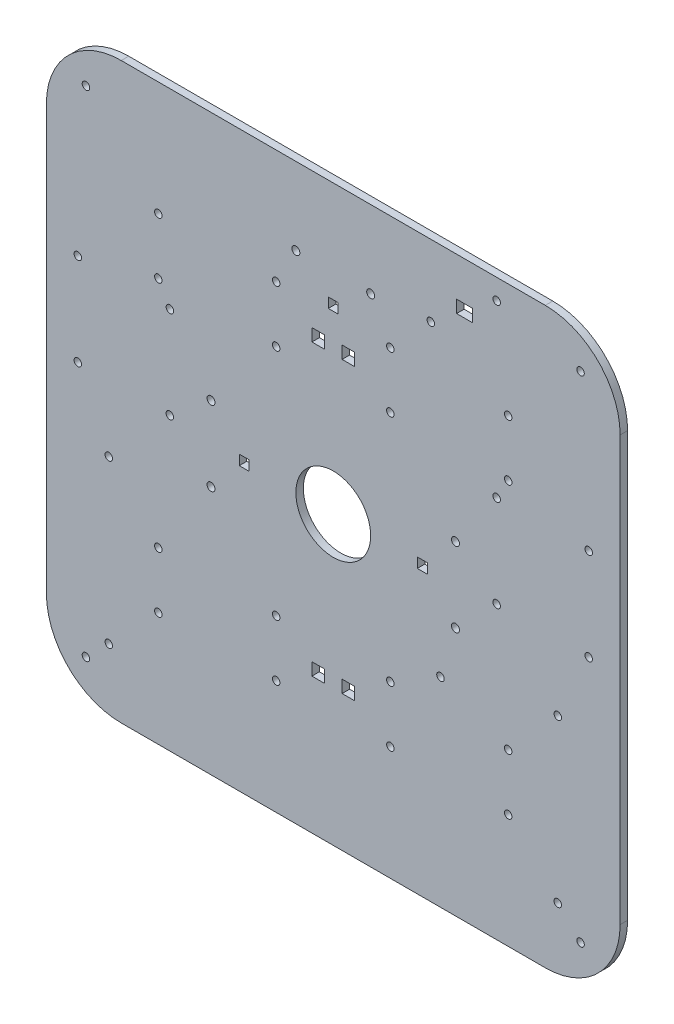
SolidWorks part; units mm, degrees
ref_plane "Alzado" through (0, 0, 0) normal (0, 0, 1) x (1, 0, 0)
ref_plane "Planta" through (0, 0, 0) normal (0, 1, 0) x (1, 0, 0)
ref_plane "Vista lateral" through (0, 0, 0) normal (1, 0, 0) x (0, 0, -1)
sketch "Croquis1" plane through (0, 0, 0) normal (0, 0, 1) x (1, 0, 0)
  line L1 (115, -115) -> (-115, -115)
  line L2 (115, -115) -> (115, 115)
  line L3 (115, 115) -> (-115, 115)
  line L4 (-115, -115) -> (-115, 115)
  line L5 (115, -115) -> (-115, 115) construction
  line L6 (115, 115) -> (-115, -115) construction
  point P0 (0, 0)
  dimension "D1" = 230
  dimension "D2" = 230
extrude "Saliente-Extruir2" add sketch "Croquis1" along normal blind 3
fillet "Redondeo1" radius 30 1 edges at (-115, 115, 1.5)
fillet "Redondeo2" radius 30 1 edges at (-115, -115, 1.5)
fillet "Redondeo3" radius 30 1 edges at (115, -115, 1.5)
fillet "Redondeo4" radius 30 1 edges at (115, 115, 1.5)
sketch "Croquis2" plane through (0, 0, 3) normal (0, 0, 1) x (1, 0, 0)
  line L14 (-3.5545, 55.5004) -> (-8.5545, 55.5004)
  line L15 (-3.5545, 55.5004) -> (-3.5545, 60.5004)
  line L16 (-3.5545, 60.5004) -> (-8.5545, 60.5004)
  line L17 (-8.5545, 55.5004) -> (-8.5545, 60.5004)
  line L21 (3.5545, 55.5004) -> (8.5545, 55.5004)
  line L22 (8.5545, 55.5004) -> (8.5545, 60.5004)
  line L23 (3.5545, 60.5004) -> (8.5545, 60.5004)
  line L24 (3.5545, 55.5004) -> (3.5545, 60.5004)
  line L25 (3.5545, -55.5004) -> (8.5545, -55.5004)
  line L26 (8.5545, -55.5004) -> (8.5545, -60.5004)
  line L27 (3.5545, -60.5004) -> (8.5545, -60.5004)
  line L28 (3.5545, -55.5004) -> (3.5545, -60.5004)
  line L29 (-3.5545, -60.5004) -> (-8.5545, -60.5004)
  line L30 (-3.5545, -55.5004) -> (-3.5545, -60.5004)
  line L31 (-3.5545, -55.5004) -> (-8.5545, -55.5004)
  line L32 (-8.5545, -55.5004) -> (-8.5545, -60.5004)
  line L64 (37.6841, -2) -> (33.6841, -2)
  line L65 (2, 70.4261) -> (-2, 70.4261)
  line L66 (2, 70.4261) -> (2, 74.4261)
  line L67 (2, 74.4261) -> (-2, 74.4261)
  line L68 (-2, 70.4261) -> (-2, 74.4261)
  line L71 (-37.6841, 2) -> (-33.6841, 2)
  line L72 (-37.6841, 2) -> (-37.6841, -2)
  line L73 (-37.6841, -2) -> (-33.6841, -2)
  line L74 (-33.6841, 2) -> (-33.6841, -2)
  line L77 (37.6841, 2) -> (37.6841, -2)
  line L78 (37.6841, 2) -> (33.6841, 2)
  line L79 (33.6841, 2) -> (33.6841, -2)
  line L90 (55.8854, 94.3793) -> (49.4598, 94.3793)
  line L91 (55.8854, 94.3793) -> (55.8854, 99.3793)
  line L92 (55.8854, 99.3793) -> (49.4598, 99.3793)
  line L93 (49.4598, 94.3793) -> (49.4598, 99.3793)
  circle A0 centre (-22.88, 46.75) radius 1.5
  circle A1 centre (-70.13, 46.75) radius 1.5
  circle A2 centre (-70.13, 69.25) radius 1.5
  circle A3 centre (-22.88, 69.25) radius 1.5
  circle A4 centre (22.88, 69.25) radius 1.5
  circle A5 centre (22.88, 46.75) radius 1.5
  circle A6 centre (70.13, 46.75) radius 1.5
  circle A7 centre (70.13, 69.25) radius 1.5
  circle A8 centre (70.13, -69.25) radius 1.5
  circle A9 centre (70.13, -46.75) radius 1.5
  circle A10 centre (22.88, -69.25) radius 1.5
  circle A11 centre (22.88, -46.75) radius 1.5
  circle A12 centre (-22.88, -46.75) radius 1.5
  circle A13 centre (-22.88, -69.25) radius 1.5
  circle A14 centre (-70.13, -69.25) radius 1.5
  circle A15 centre (-70.13, -46.75) radius 1.5
  circle A16 centre (0, 0) radius 15
  circle A17 centre (42.9733, -34.9813) radius 1.5
  circle A22 centre (-99.1421, 99.1421) radius 1.5
  circle A23 centre (99.1421, 99.1421) radius 1.5
  circle A24 centre (99.1421, -99.1421) radius 1.5
  circle A25 centre (-99.1421, -99.1421) radius 1.5
  circle A26 centre (-49, 15) radius 1.6
  circle A27 centre (-49, -15) radius 1.6
  circle A28 centre (49, 15) radius 1.6
  circle A29 centre (49, -15) radius 1.6
  circle A30 centre (15, 84) radius 1.6
  circle A31 centre (-15, 84) radius 1.6
  circle A32 centre (-102.4075, 38.45) radius 1.5
  circle A33 centre (-65.5075, 38.45) radius 1.5
  circle A34 centre (-65.5075, 1.55) radius 1.5
  circle A35 centre (-102.4075, 1.55) radius 1.5
  circle A36 centre (102.4075, 1.55) radius 1.5
  circle A37 centre (65.5075, 1.55) radius 1.5
  circle A38 centre (65.5075, 38.45) radius 1.5
  circle A39 centre (102.4075, 38.45) radius 1.5
  circle A40 centre (-90, -90) radius 1.5
  circle A41 centre (90, -90) radius 1.5
  circle A42 centre (90, -25) radius 1.5
  circle A43 centre (-90, -25) radius 1.5
  circle A44 centre (39.0956, 86.3146) radius 1.5
  circle A45 centre (65.5075, 106.8666) radius 1.5
  point P165 (0, 72.4261)
sketch "Croquis3" plane through (0, 0, 3) normal (0, 0, 1) x (1, 0, 0)
sketch "Croquis4" plane through (0, 0, 3) normal (0, 0, 1) x (1, 0, 0)
extrude "Cortar-Extruir2" cut sketch "Croquis2" against normal blind 3
